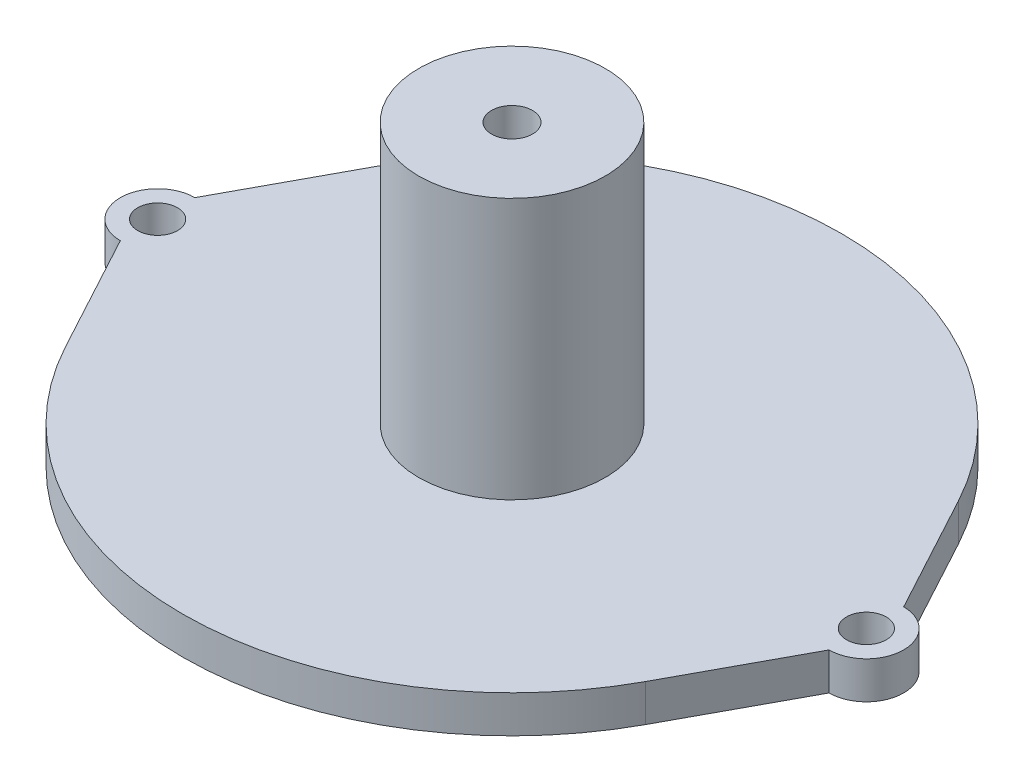
SolidWorks part; units mm, degrees
material "PLA"
ref_plane "Front Plane" through (0, 0, 0) normal (0, 0, 1) x (1, 0, 0)
ref_plane "Top Plane" through (0, 0, 0) normal (0, 1, 0) x (1, 0, 0)
ref_plane "Right Plane" through (0, 0, 0) normal (1, 0, 0) x (0, 0, -1)
sketch "Sketch1" plane through (0, 0, 0) normal (0, 1, 0) x (1, 0, 0)
  line L0 (-28.5, 3) -> (-23.3143, 12.5973)
  line L1 (-28.5, -3) -> (-23.3143, -12.5973)
  line L2 (28.5, -3) -> (23.3143, -12.5973)
  line L3 (28.5, 3) -> (23.3143, 12.5973)
  arc A0 (-23.3143, -12.5973) -> (23.3143, -12.5973) centre (0, 0) ccw
  arc A1 (28.5, -3) -> (28.5, 3) centre (28.5, 0) ccw
  arc A2 (-28.5, 3) -> (-28.5, -3) centre (-28.5, 0) ccw
  arc A3 (23.3143, 12.5973) -> (-23.3143, 12.5973) centre (0, 0) ccw
  dimension "D1" = 53
  dimension "D4" = 6
  dimension "D2" = 1
  dimension "D3" = 1
extrude "Boss-Extrude1" add sketch "Sketch1" against normal blind 3
sketch "Sketch2" plane through (0, 0, 0) normal (0, 1, 0) x (1, 0, 0)
  circle A0 centre (0, 0) radius 7.5
  dimension "D1" = 15
extrude "Boss-Extrude2" add sketch "Sketch2" along normal blind 21
hole_wizard "M3 Clearance Hole1" positions "Sketch3" profile "Sketch4" hole size "M3" standard "ANSI Metric" end condition up to next
sketch "Sketch3" plane through (0, -3, 0) normal (0, -1, 0) x (-1, 0, 0)
  point P0 (-28.5, 0)
  point P3 (28.5, 0)
sketch "Sketch4" plane through (28.5, -3, 0) normal (1, 0, 0) x (0, 0, -1)
  line L0 (0, 0) -> (0, 3)
  line L1 (0, 3) -> (1.6, 3)
  line L2 (1.6, 3) -> (1.6, 0)
  line L5 (1.6, 0) -> (0, 0)
  line L11 (0, -6.35) -> (0, 107.95) construction
  dimension "Thru Hole Dia." = 3.2
  dimension "Thru Hole Depth" = 3
sketch "Sketch5" plane through (0, 21, 0) normal (0, 1, 0) x (1, 0, 0)
  circle A0 centre (0, 0) radius 1.65
  dimension "D1" = 3.3
extrude "Cut-Extrude1" cut sketch "Sketch5" against normal through all
equation "\"D3@Sketch1\"=\"D2@Sketch1\""
